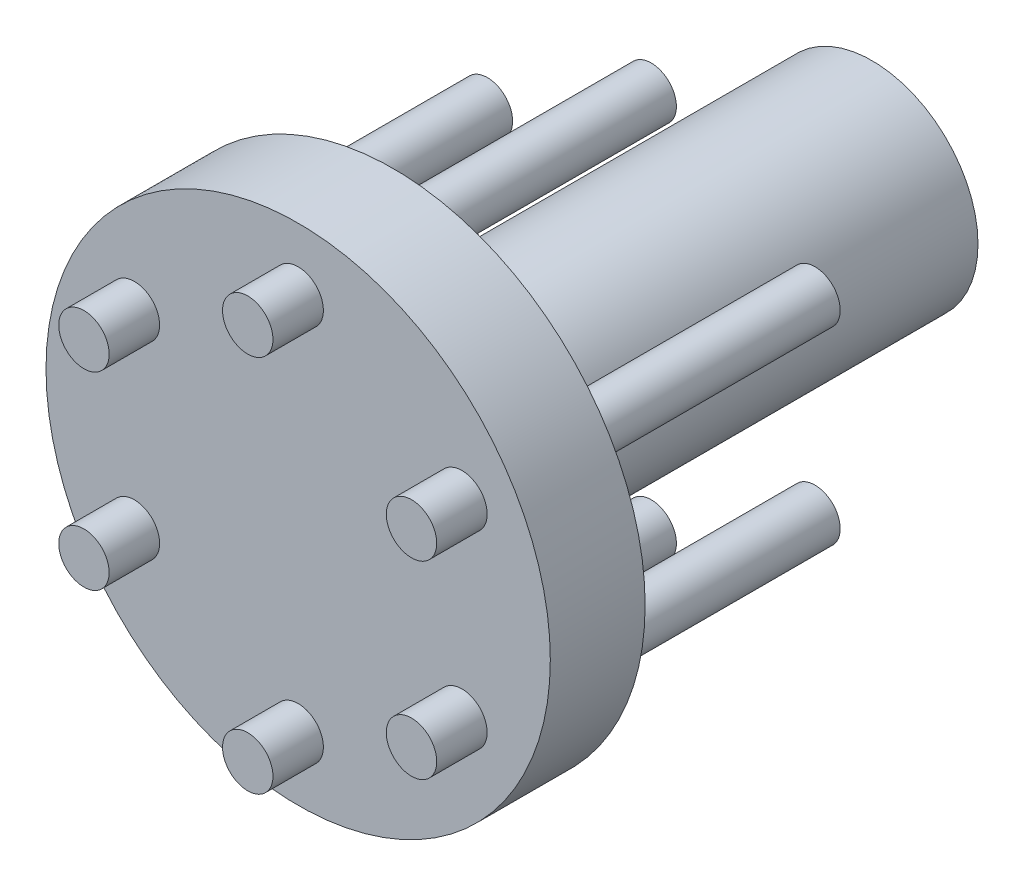
SolidWorks part; units mm, degrees
ref_plane "Front Plane" through (0, 0, 0) normal (0, 0, 1) x (1, 0, 0)
ref_plane "Top Plane" through (0, 0, 0) normal (0, 1, 0) x (1, 0, 0)
ref_plane "Right Plane" through (0, 0, 0) normal (1, 0, 0) x (0, 0, -1)
sketch "Sketch1" plane through (0, 0, 0) normal (0, 0, 1) x (1, 0, 0)
  circle A0 centre (0, 0) radius 12.7
  dimension "D1" = 25.4
extrude "Boss-Extrude1" add sketch "Sketch1" along normal blind 4.7752
sketch "Sketch2" plane through (0, 0, 0) normal (0, 0, -1) x (-1, 0, 0)
  circle A0 centre (0, 0) radius 5.334
  dimension "D1" = 10.668
extrude "Boss-Extrude2" add sketch "Sketch2" along normal blind 24.13
sketch "Sketch3" plane through (0, 0, 4.7752) normal (0, 0, 1) x (1, 0, 0)
  circle A0 centre (0, 0) radius 9.525 construction
  circle A1 centre (0, 9.525) radius 1.27
  circle A2 centre (8.2489, 4.7625) radius 1.27
  circle A3 centre (8.2489, -4.7625) radius 1.27
  circle A4 centre (0, -9.525) radius 1.27
  circle A5 centre (-8.2489, -4.7625) radius 1.27
  circle A6 centre (-8.2489, 4.7625) radius 1.27
  point P18 (0, 0)
  dimension "D1" = 19.05
  dimension "D2" = 2.54
  dimension "D3" = 6
extrude "Boss-Extrude3" add sketch "Sketch3" along normal blind 2.54 and the other way blind 17.78
sketch "Sketch4" plane through (0, 0, 4.7752) normal (0, 0, 1) x (1, 0, 0)
  line L0 (0, 12.7) -> (0, -12.7) construction
  circle A0 centre (0, 0) radius 12.7 construction
sketch "Sketch6" plane through (0, 0, 0) normal (0, 0, -1) x (-1, 0, 0)
  line L0 (0, 12.7) -> (0, -12.7) construction
  line L1 (0, 12.7) -> (0, -12.7) construction
  line L2 (0, 0) -> (6.35, 10.9985) construction
  line L3 (1.4821, 3.837) -> (2.5819, 3.202)
  line L4 (1.4821, 3.837) -> (2.7521, 6.0367)
  line L5 (2.5819, 3.202) -> (3.8519, 5.4017)
  line L6 (2.7521, 6.0367) -> (3.8519, 5.4017)
  line L7 (1.4821, 3.837) -> (3.8519, 5.4017) construction
  line L8 (2.5819, 3.202) -> (2.7521, 6.0367) construction
  line L9 (4.064, 0.635) -> (6.604, 0.635)
  line L10 (6.604, 0.635) -> (6.604, -0.635)
  line L11 (4.064, -0.635) -> (6.604, -0.635)
  line L12 (4.064, 0.635) -> (4.064, -0.635)
  line L13 (2.5819, -3.202) -> (3.8519, -5.4017)
  line L14 (3.8519, -5.4017) -> (2.7521, -6.0367)
  line L15 (1.4821, -3.837) -> (2.7521, -6.0367)
  line L16 (2.5819, -3.202) -> (1.4821, -3.837)
  line L17 (-1.4821, -3.837) -> (-2.7521, -6.0367)
  line L18 (-2.7521, -6.0367) -> (-3.8519, -5.4017)
  line L19 (-2.5819, -3.202) -> (-3.8519, -5.4017)
  line L20 (-1.4821, -3.837) -> (-2.5819, -3.202)
  line L21 (-4.064, -0.635) -> (-6.604, -0.635)
  line L22 (-6.604, -0.635) -> (-6.604, 0.635)
  line L23 (-4.064, 0.635) -> (-6.604, 0.635)
  line L24 (-4.064, -0.635) -> (-4.064, 0.635)
  line L25 (-2.5819, 3.202) -> (-3.8519, 5.4017)
  line L26 (-3.8519, 5.4017) -> (-2.7521, 6.0367)
  line L27 (-1.4821, 3.837) -> (-2.7521, 6.0367)
  line L28 (-2.5819, 3.202) -> (-1.4821, 3.837)
  circle A0 centre (0, 0) radius 12.7 construction
  circle A1 centre (0, 0) radius 5.334 construction
  point P7 (2.667, 4.6194)
  point P36 (0, 0)
  dimension "D1" = 30
  dimension "D2" = 1.27
  dimension "D3" = 2.54
  dimension "D4" = 6
extrude "Boss-Extrude4" add sketch "Sketch6" along normal blind 2.54
